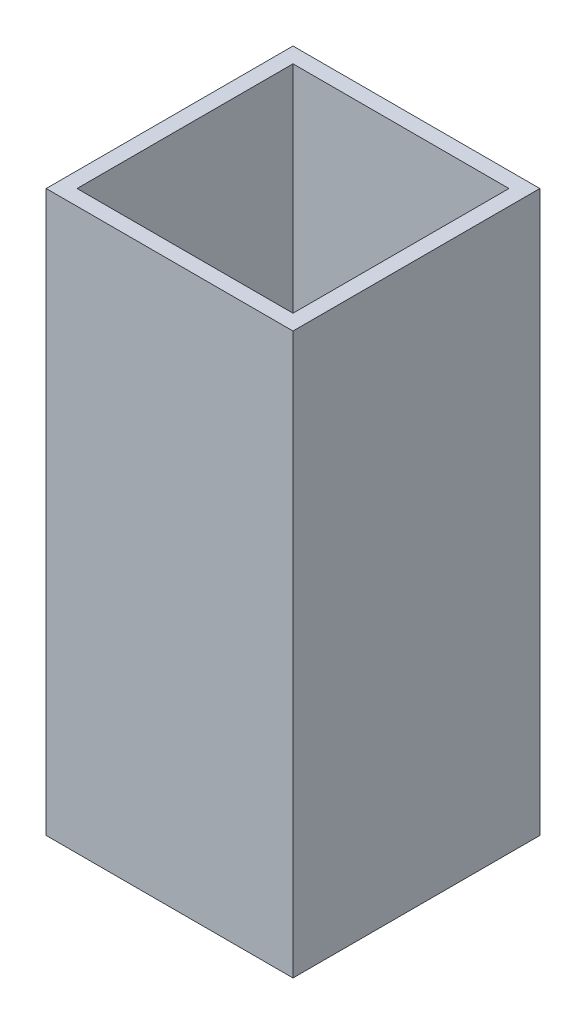
SolidWorks part; units mm, degrees
material "6061 Alloy"
ref_plane "Front Plane" through (0, 0, 0) normal (0, 0, 1) x (1, 0, 0)
ref_plane "Top Plane" through (0, 0, 0) normal (0, 1, 0) x (1, 0, 0)
ref_plane "Right Plane" through (0, 0, 0) normal (1, 0, 0) x (0, 0, -1)
sketch "Sketch1" plane through (0, 0, 0) normal (0, 1, 0) x (1, 0, 0)
  line L1 (-11.1125, -11.1125) -> (11.1125, -11.1125)
  line L2 (-11.1125, -11.1125) -> (-11.1125, 11.1125)
  line L3 (-11.1125, 11.1125) -> (11.1125, 11.1125)
  line L4 (11.1125, -11.1125) -> (11.1125, 11.1125)
  line L5 (-11.1125, -11.1125) -> (11.1125, 11.1125) construction
  line L6 (-11.1125, 11.1125) -> (11.1125, -11.1125) construction
  line L7 (-12.7, -12.7) -> (12.7, -12.7)
  line L8 (-12.7, -12.7) -> (-12.7, 12.7)
  line L9 (-12.7, 12.7) -> (12.7, 12.7)
  line L10 (12.7, -12.7) -> (12.7, 12.7)
  line L11 (-12.7, -12.7) -> (12.7, 12.7) construction
  line L12 (-12.7, 12.7) -> (12.7, -12.7) construction
  point P0 (0, 0)
  point P6 (0, 0)
  dimension "D1" = 25.4
  dimension "D2" = 1.5875
extrude "Boss-Extrude1" add sketch "Sketch1" along normal blind 57.658
